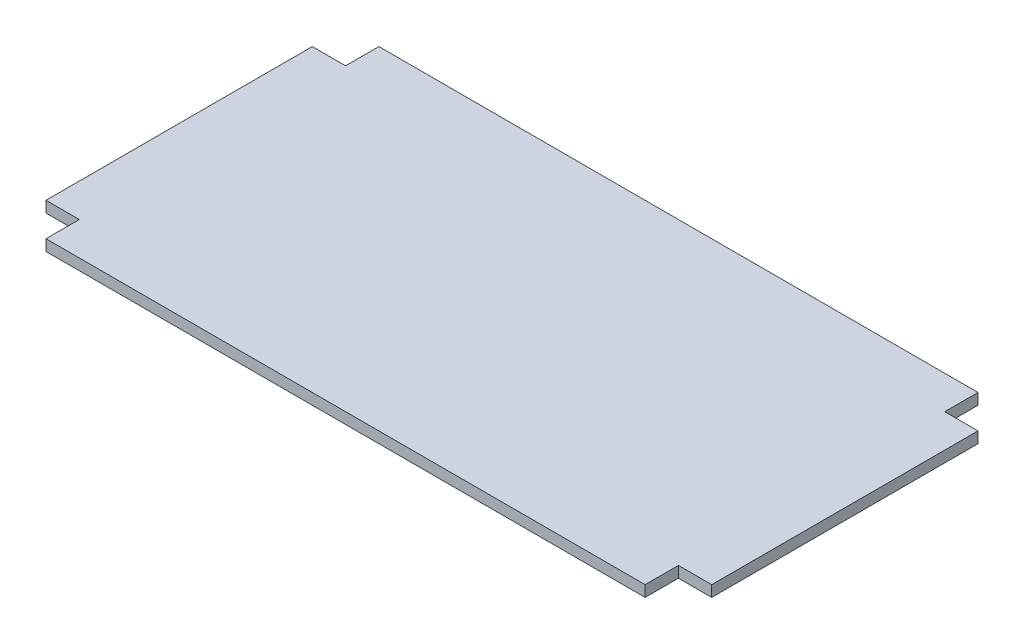
SolidWorks part; units mm, degrees
ref_plane "Front Plane" through (0, 0, 0) normal (0, 0, 1) x (1, 0, 0)
ref_plane "Top Plane" through (0, 0, 0) normal (0, 1, 0) x (1, 0, 0)
ref_plane "Right Plane" through (0, 0, 0) normal (1, 0, 0) x (0, 0, -1)
sketch "Sketch1" plane through (0, 0, 0) normal (0, 1, 0) x (1, 0, 0)
  line L0 (0, 0) -> (0, 78.2246) construction
  line L1 (-381, 190.5) -> (381, 190.5)
  line L2 (-381, 190.5) -> (-381, -190.5)
  line L3 (-381, -190.5) -> (381, -190.5)
  line L4 (381, 190.5) -> (381, -190.5)
  line L5 (-381, 190.5) -> (381, -190.5) construction
  line L6 (-381, -190.5) -> (381, 190.5) construction
  line L7 (-381, -190.5) -> (-342.9, -190.5)
  line L8 (-381, -190.5) -> (-381, -152.4)
  line L9 (-381, -152.4) -> (-342.9, -152.4)
  line L10 (-342.9, -190.5) -> (-342.9, -152.4)
  line L11 (342.9, -190.5) -> (342.9, -152.4)
  line L12 (-381, 190.5) -> (-342.9, 190.5)
  line L13 (-381, 190.5) -> (-381, 152.4)
  line L14 (-381, 152.4) -> (-342.9, 152.4)
  line L15 (-342.9, 190.5) -> (-342.9, 152.4)
  line L16 (381, -152.4) -> (342.9, -152.4)
  line L17 (342.9, 190.5) -> (342.9, 152.4)
  line L18 (381, 152.4) -> (342.9, 152.4)
  point P0 (0, 0)
  dimension "D1" = 762
  dimension "D2" = 381
  dimension "D3" = 38.1
  dimension "D4" = 38.1
  dimension "D5" = 38.1
  dimension "D6" = 38.1
extrude "Boss-Extrude1" add sketch "Sketch1" along normal blind 12.7 contours L4 L18 L17 L1 L15 L14 L2 L9 L10 L3 L11 L16
